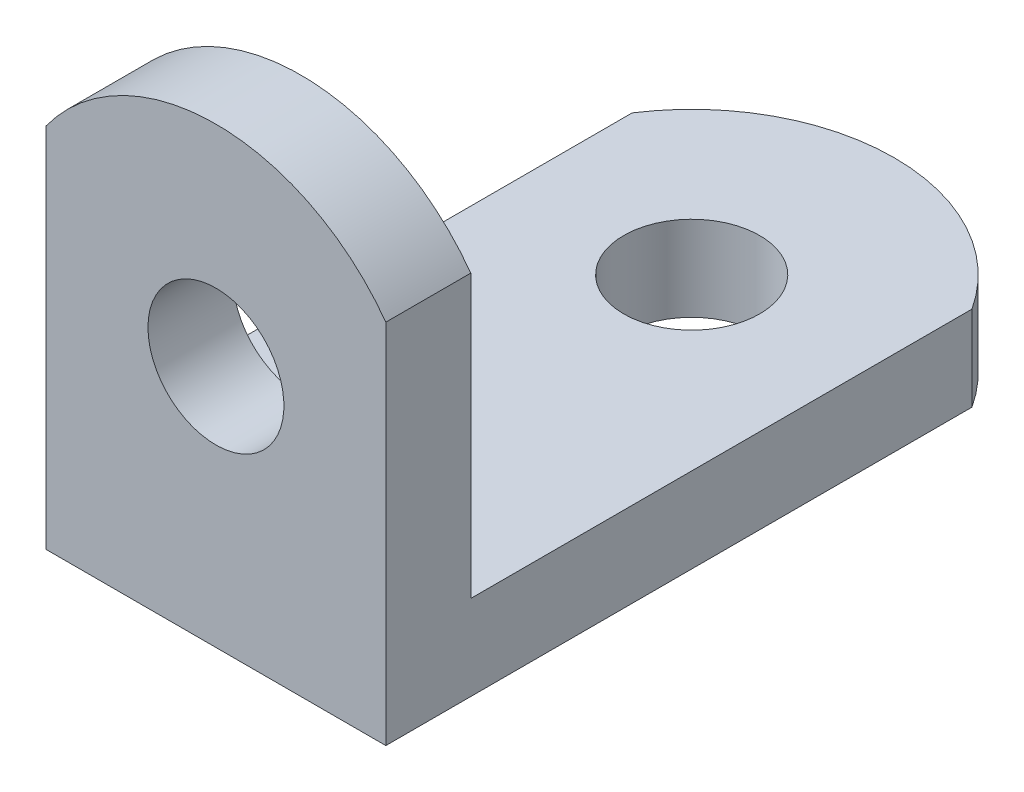
SolidWorks part; units mm, degrees
ref_plane "Front Plane" through (0, 0, 0) normal (0, 0, 1) x (1, 0, 0)
ref_plane "Top Plane" through (0, 0, 0) normal (0, 1, 0) x (1, 0, 0)
ref_plane "Right Plane" through (0, 0, 0) normal (1, 0, 0) x (0, 0, -1)
sketch "Sketch1" plane through (0, 0, 0) normal (0, 1, 0) x (1, 0, 0)
  line L1 (-25.4618, -20.5194) -> (-12.7618, -20.5194)
  line L2 (-25.4618, -20.5194) -> (-25.4618, 4.8806)
  line L3 (-25.4618, 4.8806) -> (-12.7618, 4.8806)
  line L4 (-12.7618, -20.5194) -> (-12.7618, 4.8806)
  line L5 (-25.4618, -20.5194) -> (-12.7618, 4.8806) construction
  line L6 (-25.4618, 4.8806) -> (-12.7618, -20.5194) construction
  point P0 (-19.1118, -7.8194)
  dimension "D1" = 25.4
  dimension "D2" = 12.7
extrude "Boss-Extrude1" add sketch "Sketch1" along normal blind 3.175
sketch "Sketch2" plane through (0, 3.175, 0) normal (0, 1, 0) x (1, 0, 0)
  line L0 (-12.7618, -20.5194) -> (-12.7618, 4.8806) construction
  line L1 (-25.4618, -20.5194) -> (-12.7618, -20.5194)
  line L2 (-25.4618, -20.5194) -> (-25.4618, -17.3444)
  line L3 (-25.4618, -17.3444) -> (-12.7618, -17.3444)
  line L4 (-12.7618, -20.5194) -> (-12.7618, -17.3444)
  dimension "D1" = 3.175
extrude "Boss-Extrude2" add sketch "Sketch2" along normal blind 13.7922
sketch "Sketch3" plane through (0, 3.175, 0) normal (0, 1, 0) x (1, 0, 0)
  line L0 (-12.7618, 4.8806) -> (-25.4618, 4.8806) construction
  circle A0 centre (-19.1118, -2.7394) radius 2.54
  dimension "D1" = 7.62
  dimension "D2" = 5.08
extrude "Cut-Extrude1" cut sketch "Sketch3" against normal through all
sketch "Sketch4" plane through (0, 3.175, 0) normal (0, 1, 0) x (1, 0, 0)
  line L0 (-12.7618, -17.3444) -> (-12.7618, 4.8806) construction
  line L1 (-25.4618, 4.8806) -> (-12.7618, 4.8806)
  line L2 (-25.4618, 4.8806) -> (-25.4618, 1.3851)
  line L4 (-12.7618, 4.8806) -> (-12.7618, 1.3851)
  arc A0 (-12.7618, 1.3851) -> (-25.4618, 1.3851) centre (-19.1118, -2.7394) ccw
extrude "Cut-Extrude2" cut sketch "Sketch4" against normal through all
sketch "Sketch5" plane through (0, 0, 17.3444) normal (0, 0, -1) x (-1, 0, 0)
  line L0 (12.7618, 16.9672) -> (25.4618, 16.9672) construction
  circle A0 centre (19.1118, 9.0932) radius 2.54
  dimension "D1" = 7.874
  dimension "D2" = 5.08
extrude "Cut-Extrude3" cut sketch "Sketch5" against normal through all
sketch "Sketch6" plane through (0, 0, 17.3444) normal (0, 0, -1) x (-1, 0, 0)
  line L1 (25.4618, 16.9672) -> (12.7618, 16.9672)
  line L2 (25.4618, 16.9672) -> (25.4618, 13.7044)
  line L4 (12.7618, 16.9672) -> (12.7618, 13.7044)
  arc A0 (25.4618, 13.7044) -> (12.7618, 13.7044) centre (19.1118, 9.0932) ccw
extrude "Cut-Extrude4" cut sketch "Sketch6" against normal through all
